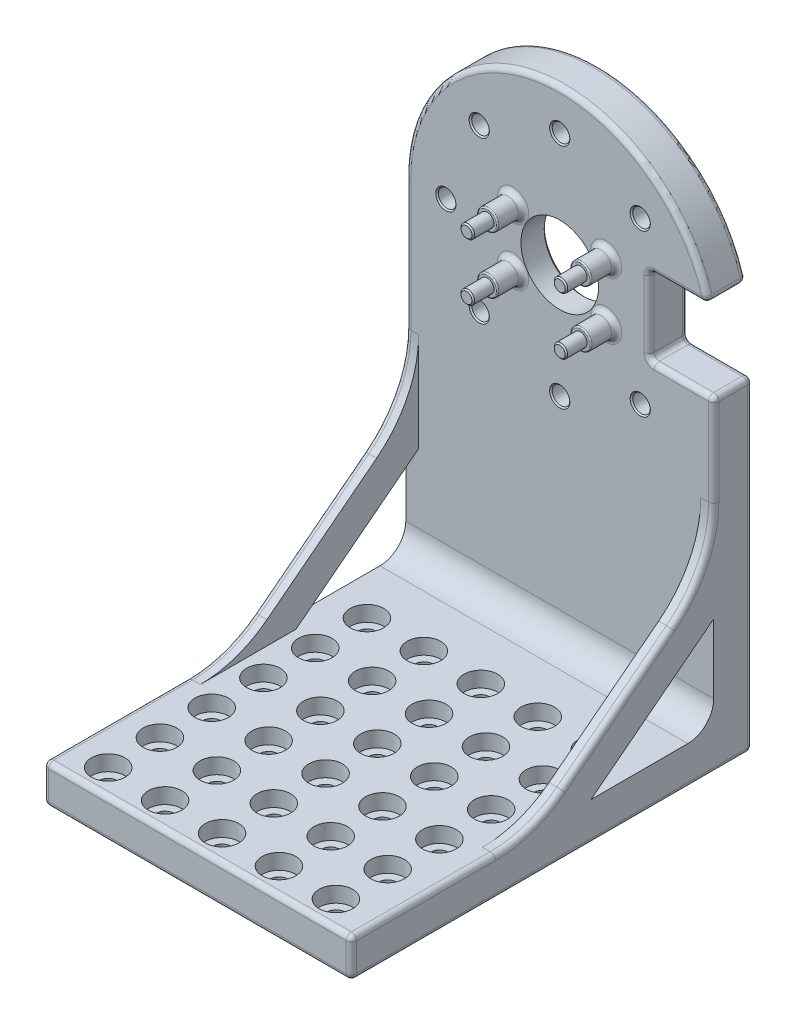
SolidWorks part; units mm, degrees
ref_plane "Front Plane" through (0, 0, 0) normal (0, 0, 1) x (1, 0, 0)
ref_plane "Top Plane" through (0, 0, 0) normal (0, 1, 0) x (1, 0, 0)
ref_plane "Right Plane" through (0, 0, 0) normal (1, 0, 0) x (0, 0, -1)
sketch "Sketch1" plane through (0, 0, 0) normal (0, 0, 1) x (1, 0, 0)
  line L1 (-29.75, -50) -> (29.75, -50)
  line L2 (-29.75, -50) -> (-29.75, 50)
  line L3 (-29.75, 50) -> (29.75, 50)
  line L4 (29.75, -50) -> (29.75, 50)
  line L5 (-29.75, -50) -> (29.75, 50) construction
  line L6 (-29.75, 50) -> (29.75, -50) construction
  point P0 (0, 0)
  dimension "D1" = 59.5
  dimension "D2" = 100
extrude "Boss-Extrude3" add sketch "Sketch1" along normal blind 7.5
sketch "Sketch7" plane through (0, 0, 7.5) normal (0, 0, 1) x (1, 0, 0)
  line L0 (29.75, 50) -> (-29.75, 50) construction
  circle A0 centre (0, 20.25) radius 7.5
  dimension "D1" = 15
  dimension "D2" = 29.75
extrude "Cut-Extrude2" cut sketch "Sketch7" against normal up to surface (7.5 mm away) up to face at (0, 0, 0)
hole_wizard "M3 Clearance Hole2" positions "Sketch8" profile "Sketch9" hole size "M3" standard "ANSI Metric"
sketch "Sketch8" plane through (0, 0, 7.5) normal (0, 0, 1) x (1, 0, 0)
  line L0 (0, 20.25) -> (0, 42.25) construction
  point P0 (0, 42.25)
  dimension "D1" = 22
sketch "Sketch9" plane through (0, 42.25, 7.5) normal (1, 0, 0) x (0, -1, 0)
  line L0 (0, 0) -> (0, 8.5215)
  line L1 (0, 8.5215) -> (1.7, 7.5)
  line L2 (1.7, 7.5) -> (1.7, 0)
  line L5 (1.7, 0) -> (0, 0)
  line L10 (0, 8.5215) -> (-1.7, 7.5) construction
  line L11 (0, -6.35) -> (0, 107.95) construction
  dimension "Hole Dia." = 3.4
  dimension "Hole Depth" = 7.5
  dimension "Drill Angle" = 118
pattern_circular "CirPattern1" count 8 every 45 about axis through (0, 20.25, 0) along (0, 0, 1) skipping 6 of "M3 Clearance Hole2"
sketch "Sketch10" plane through (0, 0, 7.5) normal (0, 0, 1) x (1, 0, 0)
  line L0 (29.75, -50) -> (29.75, 50) construction
  line L1 (29.75, 27.75) -> (17.25, 27.75)
  line L2 (29.75, 27.75) -> (29.75, 12.75)
  line L3 (29.75, 12.75) -> (17.25, 12.75)
  line L4 (17.25, 27.75) -> (17.25, 12.75)
  line L5 (-22, 20.25) -> (0, 20.25) construction
  line L6 (17.25, 20.25) -> (29.75, 20.25) construction
  dimension "D1" = 12.5
  dimension "D2" = 15
extrude "Cut-Extrude3" cut sketch "Sketch10" against normal up to surface (7.5 mm away) up to face at (13.8563, 4.6937, 0)
sketch "Sketch11" plane through (0, 0, 7.5) normal (0, 0, 1) x (1, 0, 0)
  line L0 (-29.75, 20.25) -> (-29.75, 50)
  line L1 (-29.75, 50) -> (0, 50)
  circle A0 centre (0, 20.25) radius 7.5 construction
  circle A1 centre (0, 20.25) radius 7.5 construction
  arc A2 (0, 50) -> (-29.75, 20.25) centre (0, 20.25) ccw
extrude "Cut-Extrude4" cut sketch "Sketch11" against normal up to surface (7.5 mm away) up to face at (11.75, 10.125, 0)
mirror "Mirror1" about plane through (0, 0, 0) normal (1, 0, 0) of "Cut-Extrude4"
fillet "Fillet2" radius 1 4 edges at (29.75, 12.75, 3.75) (17.25, 12.75, 3.75) (17.25, 27.75, 3.75) (28.7891, 27.75, 3.75)
sketch "Sketch12" plane through (0, 0, 7.5) normal (0, 0, 1) x (1, 0, 0)
  line L1 (-9, 14.75) -> (9, 14.75) construction
  line L2 (-9, 14.75) -> (-9, 25.75) construction
  line L3 (-9, 25.75) -> (9, 25.75) construction
  line L4 (9, 14.75) -> (9, 25.75) construction
  line L5 (-9, 14.75) -> (9, 25.75) construction
  line L6 (-9, 25.75) -> (9, 14.75) construction
  circle A0 centre (-9, 25.75) radius 1.3
  circle A1 centre (9, 25.75) radius 1.3
  circle A2 centre (9, 14.75) radius 1.3
  circle A3 centre (-9, 14.75) radius 1.3
  point P0 (0, 20.25)
  dimension "D3" = 2.6
  dimension "D4" = 2.6
  dimension "D5" = 2.6
  dimension "D6" = 2.6
  dimension "D1" = 18
  dimension "D2" = 11
extrude "Boss-Extrude4" add sketch "Sketch12" along normal blind 9
sketch "Sketch13" plane through (0, 0, 7.5) normal (0, 0, 1) x (1, 0, 0)
  circle A0 centre (-9, 14.75) radius 1.3 construction
  circle A1 centre (9, 14.75) radius 1.3 construction
  circle A2 centre (9, 25.75) radius 1.3 construction
  circle A3 centre (-9, 25.75) radius 1.3 construction
  circle A4 centre (-9, 14.75) radius 1.3
  circle A5 centre (9, 14.75) radius 1.3
  circle A6 centre (9, 25.75) radius 1.3
  circle A7 centre (-9, 25.75) radius 1.3
  circle A8 centre (-9, 25.75) radius 2
  circle A9 centre (9, 25.75) radius 2
  circle A10 centre (9, 14.75) radius 2
  circle A11 centre (-9, 14.75) radius 2
  dimension "D1" = 4
  dimension "D2" = 4
  dimension "D3" = 4
  dimension "D4" = 4
extrude "Boss-Extrude5" add sketch "Sketch13" along normal blind 5
sketch "Sketch14" plane through (0, 0, 7.5) normal (0, 0, 1) x (1, 0, 0)
  line L0 (29.75, -50) -> (29.75, 11.75) construction
  line L1 (-29.75, -50) -> (29.75, -50)
  line L2 (-29.75, -50) -> (-29.75, -42.5)
  line L3 (-29.75, -42.5) -> (29.75, -42.5)
  line L4 (29.75, -50) -> (29.75, -42.5)
  dimension "D1" = 7.5
extrude "Boss-Extrude6" add sketch "Sketch14" along normal blind 70
sketch "Sketch15" plane through (29.75, 0, 0) normal (1, 0, 0) x (0, 0, -1)
  line L0 (-7.5, -24.1229) -> (-7.5, -15.375)
  line L1 (-7.5, -42.5) -> (-7.5, 11.75) construction
  line L2 (-7.5, -15.375) -> (-42.5, -42.5)
  line L3 (-77.5, -42.5) -> (-7.5, -42.5) construction
  line L4 (-42.5, -42.5) -> (-31.2125, -42.5)
  line L5 (-7.5, -24.1229) -> (-31.2125, -42.5)
  dimension "D1" = 30
extrude "Boss-Extrude7" add sketch "Sketch15" against normal blind 2.5
mirror "Mirror2" about plane through (0, 0, 0) normal (1, 0, 0) of "Boss-Extrude7"
fillet "Fillet3" radius 21 4 edges at (-28.5, -42.5, 42.5) (28.5, -42.5, 42.5) (28.5, -15.375, 7.5) (-28.5, -15.375, 7.5)
fillet "Fillet4" radius 5 1 edges at (0, -42.5, 7.5)
hole_wizard "CBORE for M3 SHCS1" positions "Sketch17" profile "Sketch18" counterbore size "M3" standard "ANSI Metric"
sketch "Sketch17" plane through (0, -42.5, 0) normal (0, 1, 0) x (1, 0, 0)
  line L0 (-22.25, -22.5) -> (-11.25, -22.5) construction
  line L1 (-11.25, -22.5) -> (-0.25, -22.5) construction
  line L2 (-0.25, -22.5) -> (10.75, -22.5) construction
  line L3 (10.75, -22.5) -> (21.75, -22.5) construction
  line L5 (-27.25, -15.636) -> (-27.25, -36.8209) construction
  line L6 (29.75, -12.5) -> (-29.75, -12.5) construction
  point P0 (-22.25, -22.5)
  point P2 (-11.25, -22.5)
  point P4 (-0.25, -22.5)
  point P6 (10.75, -22.5)
  point P8 (21.75, -22.5)
  dimension "D2" = 11
  dimension "D1" = 11
  dimension "D3" = 11
  dimension "D4" = 11
  dimension "D5" = 5
  dimension "D6" = 10
sketch "Sketch18" plane through (-22.25, -42.5, 22.5) normal (1, 0, 0) x (0, 0, 1)
  line L0 (0, 0) -> (0, 8.5215)
  line L1 (0, 8.5215) -> (1.7, 7.5)
  line L2 (1.7, 7.5) -> (1.7, 3)
  line L3 (1.7, 3) -> (3.25, 3)
  line L4 (3.25, 3) -> (3.25, 0)
  line L5 (3.25, 0) -> (0, 0)
  line L10 (0, 8.5215) -> (-1.7, 7.5) construction
  line L11 (0, -6.35) -> (0, 107.95) construction
  dimension "Hole Dia." = 3.4
  dimension "Hole Depth" = 7.5
  dimension "C'Bore Dia." = 6.5
  dimension "C'Bore Depth" = 3
  dimension "Drill Angle" = 118
pattern_linear "LPattern1" count 6 spacing 10 along (0, 0, 1) of "CBORE for M3 SHCS1"
fillet "Fillet5" radius 1 65 edges at (-29.75, -42.5, 63.5925) (-29.75, -41.3692, 42.8869) (-29.75, -29.8896, 26.2285) (-29.75, -14.3244, 9.6434) (-29.75, 7.5842, 7.5) (29.75, -42.5, 63.5925) (29.75, -41.3692, 42.8869) (29.75, -29.8896, 26.2285) (29.75, -14.3244, 9.6434) (29.75, 3.3342, 7.5) (29.4571, 12.4571, 7.5) (23.5, 12.75, 7.5) (17.5429, 13.0429, 7.5) (17.25, 20.25, 7.5) (17.5429, 27.4571, 7.5) (22.8574, 27.75, 7.5) (28.2696, 28.1566, 7.5) (-29.75, -14.875, 0) (-4.4478, 49.6656, 0) (28.2696, 28.1566, 0) (22.8574, 27.75, 0) (17.5429, 27.4571, 0) (17.25, 20.25, 0) (17.5429, 13.0429, 0) (23.5, 12.75, 0) (29.4571, 12.4571, 0) (-11.25, -50, 74.2) (-11.25, -50, 64.2) (-11.25, -50, 54.2) (-11.25, -50, 44.2) (-0.25, -50, 74.2) (-0.25, -50, 64.2) (-0.25, -50, 54.2) (-0.25, -50, 44.2) (10.75, -50, 74.2) (10.75, -50, 64.2) (10.75, -50, 54.2) (10.75, -50, 44.2) (21.75, -50, 74.2) (21.75, -50, 64.2) (21.75, -50, 54.2) (21.75, -50, 44.2) (-22.25, -50, 74.2) (-22.25, -50, 64.2) (-22.25, -50, 54.2) (-22.25, -50, 44.2) (-22.25, -50, 24.2) (-11.25, -50, 24.2) (-0.25, -50, 24.2) (10.75, -50, 24.2) (21.75, -50, 24.2) (-29.75, -50, 38.75) (0, -50, 77.5) (29.75, -50, 38.75) (0, -50, 0) (-22.25, -50, 34.2) (21.75, -50, 34.2) (10.75, -50, 34.2) (-0.25, -50, 34.2) (-11.25, -50, 34.2) (-4.4478, 49.6656, 7.5) (29.75, -19.125, 0) (-29.75, -46.25, 77.5) (29.75, -46.25, 77.5) (0, -42.5, 77.5)
chamfer "Chamfer1" [suppressed] distance 1 angle 45
fillet "Fillet6" radius 1 4 edges at (-11, 25.75, 7.5) (-11, 14.75, 7.5) (7, 14.75, 7.5) (7, 25.75, 7.5)
fillet "Fillet7" radius 0.25 4 edges at (11, 14.75, 12.5) (-7, 14.75, 12.5) (11, 25.75, 12.5) (-7, 25.75, 12.5)
chamfer "Chamfer2" distance 0.25 angle 45 4 edges at (-7.7, 14.75, 16.5) (10.3, 14.75, 16.5) (10.3, 25.75, 16.5) (-7.7, 25.75, 16.5)
chamfer "Chamfer3" distance 0.25 angle 45 8 edges at (-13.8563, 4.6937, 7.5) (-17.2563, 4.6937, 0) (17.2563, 4.6937, 7.5) (1.7, -1.75, 7.5) (-20.3, 20.25, 7.5) (-13.8563, 35.8063, 7.5) (1.7, 42.25, 7.5) (17.2563, 35.8063, 7.5)
sketch "Sketch19" plane through (0, 0, 0) normal (0, 0, -1) x (-1, 0, 0)
  circle A0 centre (0, 20.25) radius 15
  circle A1 centre (0, 20.25) radius 7.5 construction
  circle A2 centre (0, 20.25) radius 7.5
  dimension "D1" = 30
extrude "Cut-Extrude5" cut sketch "Sketch19" against normal blind 2.5
chamfer "Chamfer4" distance 0.5 angle 45 3 edges at (-7.5, 20.25, 2.5) (-15, 20.25, 2.5) (-15, 20.25, 0)
equation "\"D4@Sketch12\"=\"D3@Sketch12\""
equation "\"D5@Sketch12\"=\"D3@Sketch12\""
equation "\"D6@Sketch12\"=\"D3@Sketch12\""
equation "\"D2@Sketch13\"=\"D1@Sketch13\""
equation "\"D3@Sketch13\"=\"D1@Sketch13\""
equation "\"D4@Sketch13\"=\"D1@Sketch13\""
equation "\"D2@Sketch17\"=\"D1@Sketch17\""
equation "\"D3@Sketch17\"=\"D1@Sketch17\""
equation "\"D4@Sketch17\"=\"D1@Sketch17\""
